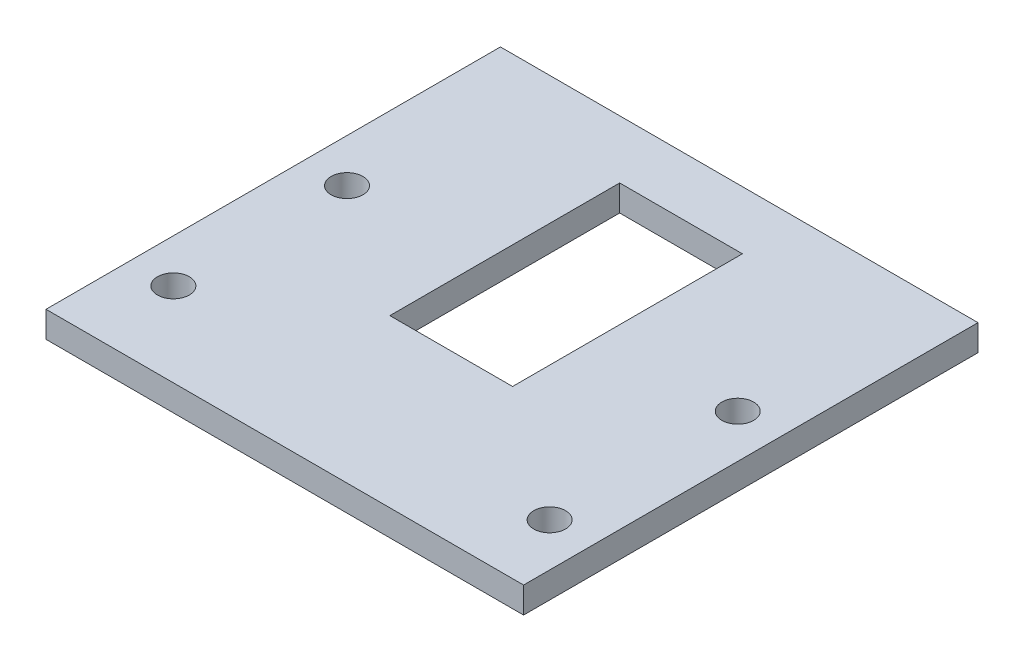
SolidWorks part; units mm, degrees
ref_plane "Front Plane" through (0, 0, 0) normal (0, 0, 1) x (1, 0, 0)
ref_plane "Top Plane" through (0, 0, 0) normal (0, 1, 0) x (1, 0, 0)
ref_plane "Right Plane" through (0, 0, 0) normal (1, 0, 0) x (0, 0, -1)
sketch "Sketch5" plane through (0, 0, 0) normal (0, 1, 0) x (1, 0, 0)
  line L0 (0, 0) -> (-41.91, 0)
  line L1 (-41.91, 0) -> (-41.91, -39.878)
  line L2 (-41.91, -39.878) -> (0, -39.878)
  line L3 (0, -39.878) -> (0, 0)
  line L4 (-41.91, -39.878) -> (-38.1, -39.878) construction
  line L5 (-38.1, -39.878) -> (-38.1, -32.512) construction
  line L6 (-20.955, -39.878) -> (-20.955, 0) construction
  line L7 (-38.1, -39.878) -> (-38.1, -17.272) construction
  line L8 (-3.81, -33.782) -> (-3.81, -39.878) construction
  line L9 (-3.81, -33.782) -> (-3.81, -17.272) construction
  circle A0 centre (-38.1, -17.272) radius 1.397
  circle A1 centre (-38.1, -32.512) radius 1.397
  circle A2 centre (-3.81, -33.782) radius 1.397
  circle A3 centre (-3.81, -17.272) radius 1.397
extrude "Extrude3" add sketch "Sketch5" along normal blind 2.286 separate body
sketch "Sketch6" plane through (0, 2.286, 0) normal (0, 1, 0) x (-1, 0, 0)
  line L0 (15.5702, 15.1892) -> (26.3398, 15.1892) construction
  line L1 (18.1927, 18.415) -> (23.7173, 18.415) construction
  line L2 (23.7173, 18.415) -> (23.7173, 21.463) construction
  line L3 (18.1927, 21.463) -> (23.7173, 18.415) construction
  line L4 (23.7173, 21.463) -> (18.1927, 18.415) construction
  line L5 (20.955, 19.939) -> (20.955, 15.1892) construction
  line L6 (20.955, 39.878) -> (20.955, 15.1892) construction
  line L7 (20.955, 5.1054) -> (15.5702, 5.1054) construction
  line L8 (41.91, 39.878) -> (0, 39.878) construction
  line L9 (26.3398, 25.273) -> (15.5702, 25.273)
  line L10 (26.3398, 25.273) -> (26.3398, 5.1054)
  line L11 (26.3398, 5.1054) -> (15.5702, 5.1054)
  line L12 (15.5702, 25.273) -> (15.5702, 5.1054)
  line L15 (18.1927, 21.463) -> (23.7173, 21.463) construction
  line L16 (18.1927, 18.415) -> (18.1927, 21.463) construction
extrude "Extrude4" cut sketch "Sketch6" against normal through all
